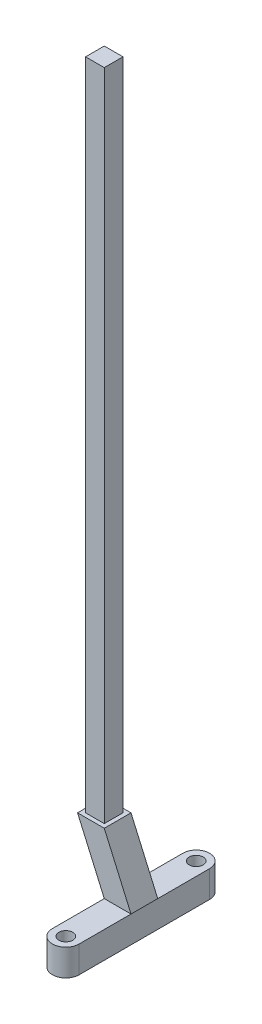
SolidWorks part; units mm, degrees
ref_plane "Front Plane" through (0, 0, 0) normal (0, 0, 1) x (1, 0, 0)
ref_plane "Top Plane" through (0, 0, 0) normal (0, 1, 0) x (1, 0, 0)
ref_plane "Right Plane" through (0, 0, 0) normal (1, 0, 0) x (0, 0, -1)
sketch "Sketch1" plane through (0, 0, 0) normal (0, 0, 1) x (1, 0, 0)
  line L0 (0, 0) -> (6.35, 0)
  line L1 (6.35, 0) -> (0, 14.478)
  line L2 (0, 14.478) -> (-6.35, 14.478)
  line L3 (-6.35, 14.478) -> (0, 0)
  dimension "D1" = 14.478
  dimension "D2" = 12.7
  dimension "D3" = 6.35
extrude "Boss-Extrude1" add sketch "Sketch1" along normal blind 6.35
sketch "Sketch2" plane through (0, 0, 0) normal (0, -1, 0) x (1, 0, 0)
  line L0 (3.175, 18.669) -> (3.175, -12.319) construction
  line L1 (6.35, 18.669) -> (6.35, -12.319)
  line L2 (0, 18.669) -> (0, -12.319)
  line L3 (6.35, 6.35) -> (6.35, 0) construction
  line L4 (0, 6.35) -> (6.35, 6.35) construction
  line L5 (0, 6.35) -> (0, 0) construction
  arc A0 (6.35, 18.669) -> (0, 18.669) centre (3.175, 18.669) ccw
  arc A1 (0, -12.319) -> (6.35, -12.319) centre (3.175, -12.319) ccw
  circle A2 centre (3.175, 18.669) radius 1.651
  circle A3 centre (3.175, -12.319) radius 1.651
  point P2 (3.175, 3.175)
  point P10 (6.35, 3.175)
  point P13 (3.175, 6.35)
  dimension "D2" = 3.302
  dimension "D1" = 30.988
extrude "Boss-Extrude2" add sketch "Sketch2" along normal blind 6.35
sketch "Sketch4" plane through (0, 14.478, 0) normal (0, 1, 0) x (1, 0, 0)
  line L0 (0, -6.35) -> (-6.35, -6.35) construction
  line L1 (-0.9525, -5.3975) -> (-5.3975, -5.3975)
  line L2 (-0.9525, -5.3975) -> (-0.9525, -0.9525)
  line L3 (-0.9525, -0.9525) -> (-5.3975, -0.9525)
  line L4 (-5.3975, -5.3975) -> (-5.3975, -0.9525)
  line L5 (0, -6.35) -> (0, 0) construction
  point P4 (-3.175, -5.3975)
  point P7 (-3.175, -6.35)
  point P8 (-0.9525, -3.175)
  point P11 (0, -3.175)
  dimension "D1" = 4.445
extrude "Boss-Extrude3" add sketch "Sketch4" along normal blind 155.575
